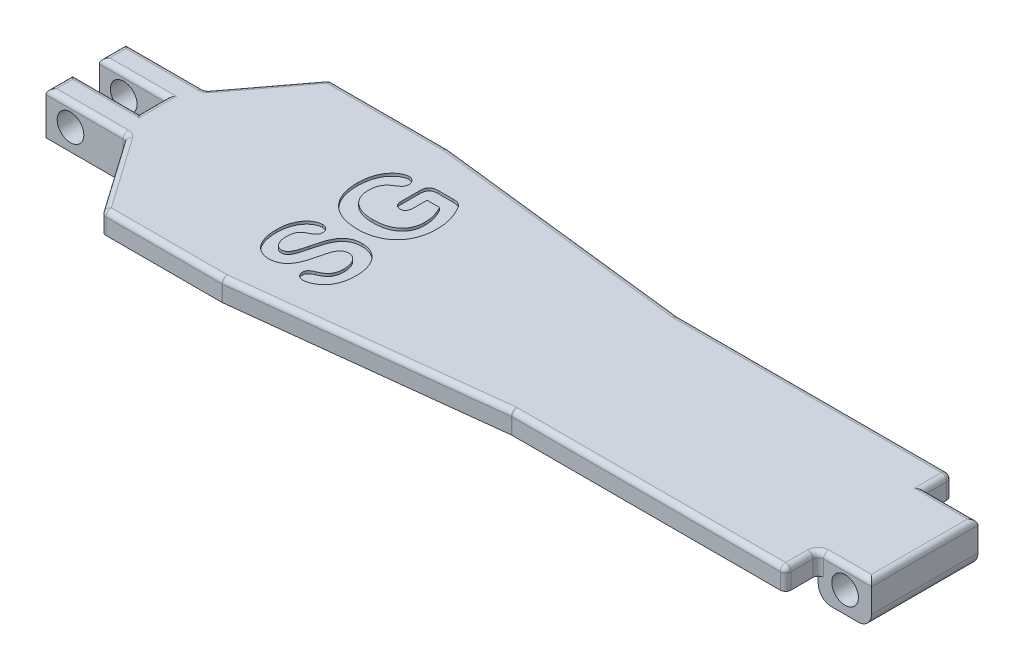
SolidWorks part; units mm, degrees
ref_plane "Front Plane" through (0, 0, 0) normal (0, 0, 1) x (1, 0, 0)
ref_plane "Top Plane" through (0, 0, 0) normal (0, 1, 0) x (1, 0, 0)
ref_plane "Right Plane" through (0, 0, 0) normal (1, 0, 0) x (0, 0, -1)
sketch "Sketch1" plane through (0, 0, 0) normal (0, 1, 0) x (1, 0, 0)
  line L0 (-14.4586, 43.5) -> (344.3411, 43.5) construction
  line L1 (50, 0) -> (94.6875, 0)
  line L2 (0, 28.5) -> (0, 38.5)
  line L3 (50, 85) -> (94.6875, 85)
  line L4 (315, 23.5) -> (315, 63.5)
  line L5 (192.1875, 73.75) -> (295, 73.75)
  line L6 (295, 73.75) -> (295, 63.5)
  line L7 (315, 63.5) -> (295, 63.5)
  line L8 (315, 23.5) -> (295, 23.5)
  line L9 (192.1875, 73.75) -> (94.6875, 85)
  line L10 (192.1875, 11.25) -> (94.6875, 0)
  line L11 (25, 38.5) -> (0, 38.5)
  line L12 (25, 48.5) -> (0, 48.5)
  line L13 (0, 58.5) -> (30, 58.5)
  line L14 (30, 28.5) -> (0, 28.5)
  line L15 (30, 28.5) -> (50, 0)
  line L16 (30, 58.5) -> (50, 85)
  line L17 (25, 48.5) -> (25, 38.5)
  line L18 (0, 48.5) -> (0, 58.5)
  line L19 (295, 23.5) -> (295, 11.25)
  line L20 (295, 11.25) -> (192.1875, 11.25)
  dimension "D3" = 20
  dimension "D4" = 20
  dimension "D5" = 20
  dimension "D6" = 20
  dimension "D9" = 5
  dimension "D10" = 5
  dimension "D11" = 30
  dimension "D12" = 30
  dimension "D14" = 10
  dimension "D15" = 10
  dimension "D16" = 25
extrude "Boss-Extrude1" add sketch "Sketch1" along normal blind 8
sketch "Sketch2" plane through (0, 0, 0) normal (0, -1, 0) x (1, 0, 0)
  line L0 (0, -48.5) -> (0, -58.5)
  line L1 (295, -23.5) -> (315, -23.5)
  line L2 (295, -23.5) -> (295, -63.5)
  line L3 (295, -63.5) -> (315, -63.5)
  line L4 (315, -23.5) -> (315, -63.5)
  line L5 (0, -28.5) -> (30, -28.5)
  line L6 (0, -28.5) -> (0, -38.5)
  line L7 (0, -58.5) -> (30, -58.5)
  line L8 (30, -28.5) -> (30, -58.5)
  line L9 (25, -48.5) -> (0, -48.5)
  line L10 (25, -48.5) -> (25, -38.5)
  line L11 (25, -38.5) -> (0, -38.5)
extrude "Boss-Extrude2" add sketch "Sketch2" along normal blind 8
sketch "Sketch3" plane through (0, 0, -23.5) normal (0, 0, 1) x (1, 0, 0)
  circle A0 centre (305.0782, 0) radius 5
  circle A1 centre (9.1969, 0) radius 5
  dimension "D1" = 10
  dimension "D2" = 10
extrude "Cut-Extrude1" cut sketch "Sketch3" against normal through all
fillet "Fillet1" radius 2 31 edges at (305, 8, -63.5) (315, 8, -43.5) (305, 8, -23.5) (295, 8, -17.375) (243.5938, 8, -11.25) (143.4375, 8, -5.625) (72.3438, 8, 0) (40, 8, -14.25) (15, 8, -28.5) (0, 8, -33.5) (12.5, 8, -38.5) (25, 8, -43.5) (12.5, 8, -48.5) (0, 8, -53.5) (15, 8, -58.5) (40, 8, -71.75) (72.3438, 8, -85) (143.4375, 8, -79.375) (243.5938, 8, -73.75) (295, 8, -68.625) (30, 4, -58.5) (50, 4, -85) (94.6875, 4, -85) (192.1875, 4, -73.75) (295, 4, -73.75) (295, 4, -23.5) (295, 4, -11.25) (192.1875, 4, -11.25) (30, 4, -28.5) (50, 4, 0) (94.6875, 4, 0)
fillet "Fillet2" radius 5 2 edges at (295, -8, -43.5) (315, -8, -43.5)
sketch "Sketch4" plane through (0, 8, 0) normal (0, 1, 0) x (1, 0, 0)
  line L0 (118.7274, 12.1452) -> (118.7274, 71.8345) construction
  text T0 "SG" font "Arial Rounded MT Bold" height 30
extrude "Cut-Extrude2" cut sketch "Sketch4" against normal blind 1
